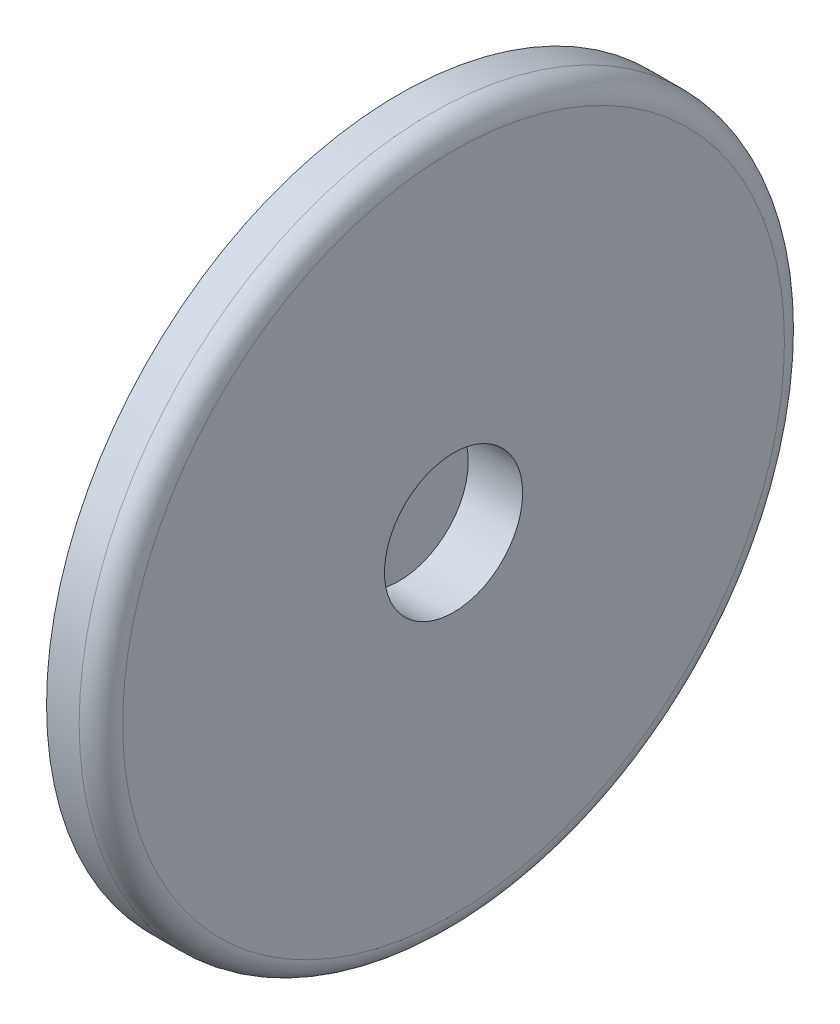
SolidWorks part; units mm, degrees
material "6061 Alloy"
ref_plane "Front Plane" through (0, 0, 0) normal (0, 0, 1) x (1, 0, 0)
ref_plane "Top Plane" through (0, 0, 0) normal (0, 1, 0) x (1, 0, 0)
ref_plane "Right Plane" through (0, 0, 0) normal (1, 0, 0) x (0, 0, -1)
sketch "Sketch1" plane through (0, 0, 0) normal (1, 0, 0) x (0, 0, -1)
  circle A0 centre (0, 0) radius 51.15
  dimension "D1" = 102.3
extrude "Boss-Extrude1" add sketch "Sketch1" along normal blind 10
sketch "Sketch2" plane through (10, 0, 0) normal (1, 0, 0) x (0, 0, -1)
  circle A0 centre (0, 0) radius 64.8486
extrude "Boss-Extrude2" add sketch "Sketch2" along normal blind 10
sketch "Sketch3" plane through (20, 0, 0) normal (1, 0, 0) x (0, 0, -1)
  circle A0 centre (0, 0) radius 12.7
  dimension "D1" = 25.4
extrude "Cut-Extrude1" cut sketch "Sketch3" against normal blind 10
fillet "Fillet1" radius 1 1 edges at (0, 0, -51.15)
fillet "Fillet2" radius 4 1 edges at (20, 0, -64.8486)
